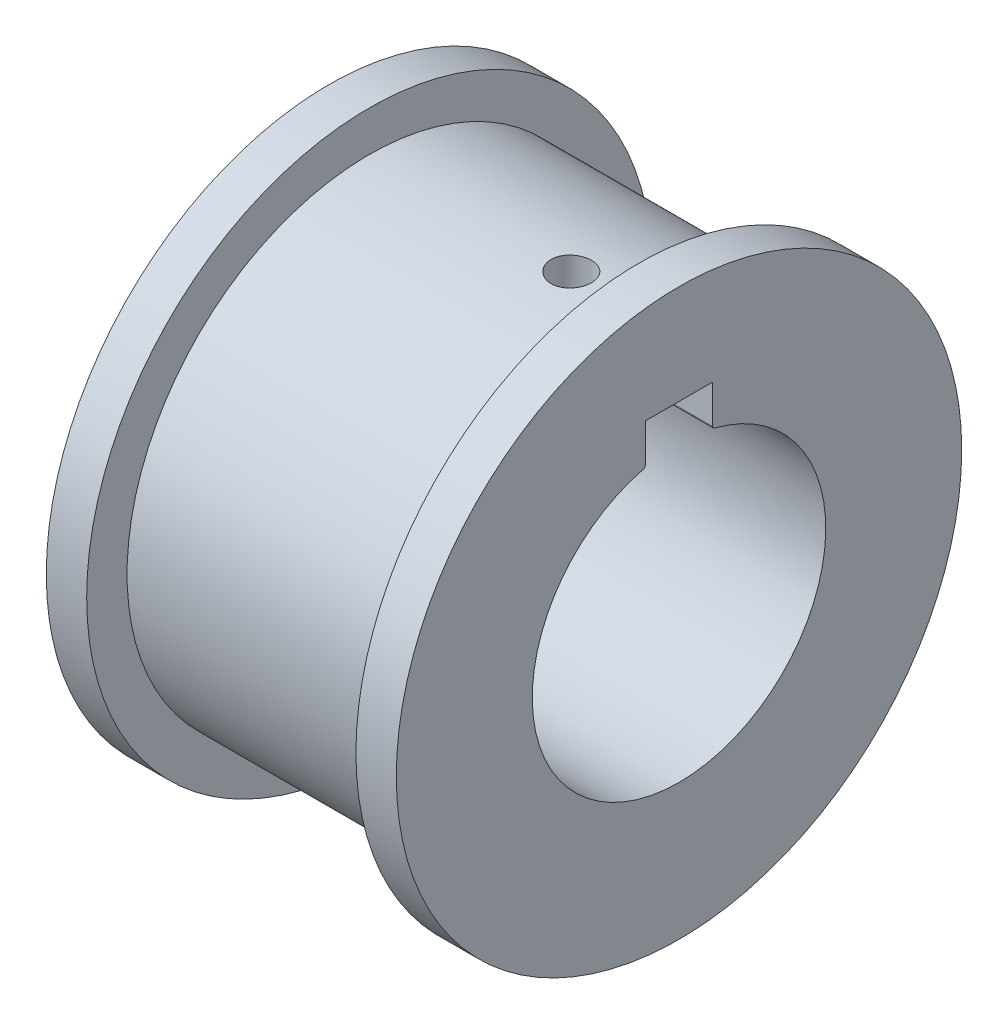
SolidWorks part; units mm, degrees
ref_plane "Piano frontale" through (0, 0, 0) normal (0, 0, 1) x (1, 0, 0)
ref_plane "Piano superiore" through (0, 0, 0) normal (0, 1, 0) x (1, 0, 0)
ref_plane "Piano destro" through (0, 0, 0) normal (1, 0, 0) x (0, 0, -1)
sketch "Sketch1" plane through (0, 0, 0) normal (1, 0, 0) x (0, 0, -1)
  circle A0 centre (0, 0) radius 18
  dimension "D1" = 36
extrude "Boss-Extrude1" add sketch "Sketch1" along normal blind 20
sketch "Sketch2" plane through (20, 0, 0) normal (1, 0, 0) x (0, 0, -1)
  line L0 (0, 4.7697) -> (0, 18) construction
  line L1 (0, 13.6094) -> (0, 4.7697) construction
  line L2 (-2.5, 13.6094) -> (2.5, 13.6094)
  line L3 (-2.5, 13.6094) -> (-2.5, 10.7666)
  line L5 (2.5, 13.6094) -> (2.5, 10.7666)
  arc A0 (-2.6514, 10.5726) -> (2.6514, 10.5726) centre (0, 0) ccw
  circle A1 centre (0, 0) radius 18 construction
  arc A2 (-2.6514, 10.5726) -> (-2.5, 10.7666) centre (-2.7, 10.7666) ccw
  arc A3 (2.6514, 10.5726) -> (2.5, 10.7666) centre (2.7, 10.7666) cw
  point P14 (-2.5, 10.6094)
  dimension "D1" = 21.8
  dimension "D4" = 0.2
  dimension "D5" = 0.2
  dimension "D2" = 5
  dimension "D3" = 3
sketch "Sketch3" plane through (20, 0, 0) normal (1, 0, 0) x (0, 0, -1)
  circle A0 centre (0, 0) radius 21
  dimension "D1" = 42
extrude "Boss-Extrude2" add sketch "Sketch3" along normal blind 3
sketch "Sketch4" plane through (0, 0, 0) normal (-1, 0, 0) x (0, 0, 1)
  circle A0 centre (0, 0) radius 21
  dimension "D1" = 42
extrude "Boss-Extrude3" add sketch "Sketch4" along normal blind 3
extrude "Cut-Extrude2" cut sketch "Sketch2" against normal blind 25 and the other way blind 3
sketch "Sketch6" plane through (0, 13.6094, 0) normal (0, -1, 0) x (1, 0, 0)
  line L0 (-3, 0) -> (23, 0) construction
  line L1 (-3, -2.5) -> (-3, 2.5) construction
  line L2 (23, -2.5) -> (23, 2.5) construction
  circle A0 centre (15, 0) radius 1.5
  dimension "D1" = 3
  dimension "D2" = 8
extrude "Cut-Extrude3" cut sketch "Sketch6" against normal blind 20
